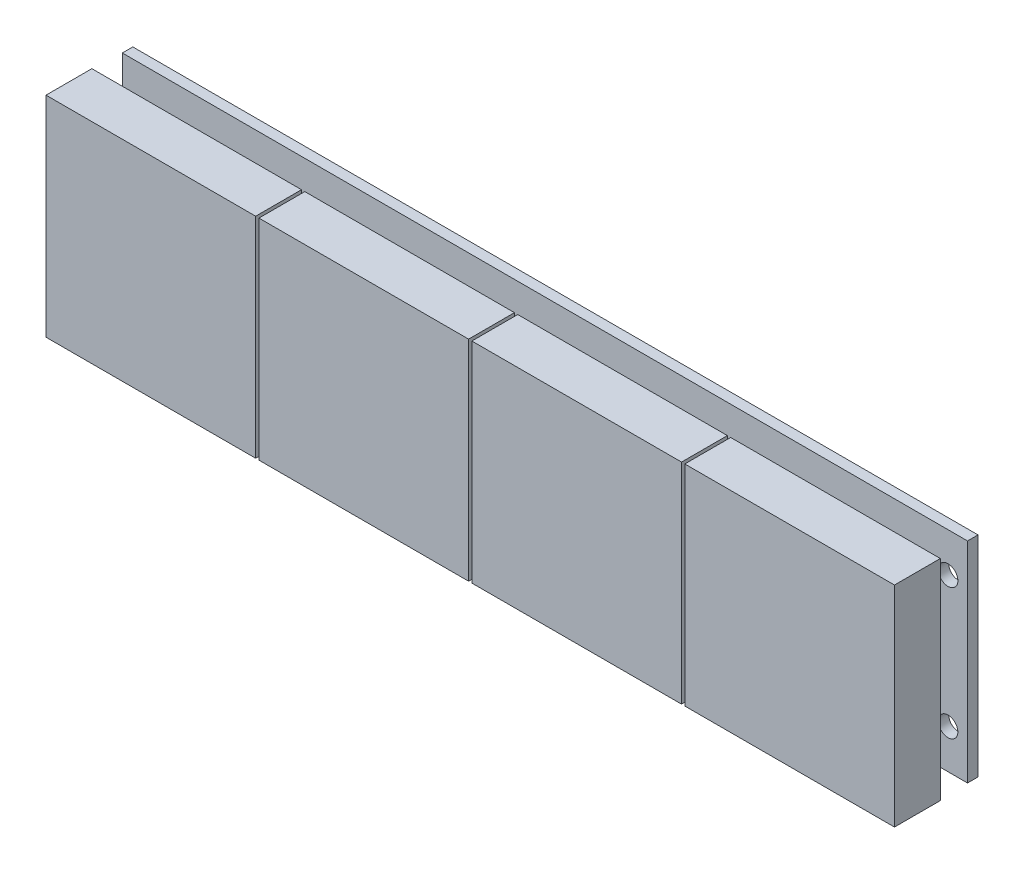
SolidWorks part; units mm, degrees
material "ABS"
ref_plane "TOP" through (0, 0, 0) normal (0, 0, 1) x (1, 0, 0)
ref_plane "FRONT" through (0, 0, 0) normal (0, 1, 0) x (1, 0, 0)
ref_plane "RIGHT" through (0, 0, 0) normal (1, 0, 0) x (0, 0, -1)
sketch "Эскиз1" plane through (0, 0, 0) normal (0, 0, 1) x (1, 0, 0)
  line L0 (-2.975, 10) -> (0, 10) construction
  line L1 (-64.5, 16) -> (64.5, 16)
  line L2 (-64.5, 16) -> (-64.5, -16)
  line L3 (-64.5, -16) -> (64.5, -16)
  line L4 (64.5, 16) -> (64.5, -16)
  line L5 (0, -16) -> (0, 16) construction
  line L6 (-64.5, 0) -> (64.5, 0) construction
  line L7 (-61.525, 10) -> (-35.225, 10) construction
  line L8 (-61.525, 10) -> (-61.525, -10) construction
  line L9 (-61.525, -10) -> (-35.225, -10) construction
  line L10 (-35.225, 10) -> (-35.225, -10) construction
  line L11 (-48.375, -10) -> (-48.375, 10) construction
  line L12 (61.525, 10) -> (64.5, 10) construction
  circle A1 centre (-61.525, 10) radius 1.5
  circle A2 centre (-61.525, -10) radius 1.5
  circle A3 centre (-35.225, -10) radius 1.5
  circle A4 centre (-35.225, 10) radius 1.5
  circle A5 centre (-29.275, 10) radius 1.5
  circle A6 centre (-29.275, -10) radius 1.5
  circle A7 centre (-2.975, 10) radius 1.5
  circle A8 centre (-2.975, -10) radius 1.5
  circle A9 centre (2.975, 10) radius 1.5
  circle A10 centre (2.975, -10) radius 1.5
  circle A11 centre (29.275, 10) radius 1.5
  circle A12 centre (29.275, -10) radius 1.5
  circle A13 centre (35.225, 10) radius 1.5
  circle A14 centre (35.225, -10) radius 1.5
  circle A15 centre (61.525, 10) radius 1.5
  circle A16 centre (61.525, -10) radius 1.5
  point P11 (-35.225, 0)
  point P36 (0, 0)
  dimension "D3" = 20
  dimension "D5" = 3
  dimension "D1" = 32
  dimension "D2" = 129
  dimension "D4" = 26.3
  dimension "D6" = 4
extrude "Бобышка-Вытянуть1" add sketch "Эскиз1" along normal blind 1.6
sketch "Эскиз2" plane through (0, 0, 1.6) normal (0, 0, 1) x (1, 0, 0)
  line L0 (-64.5, 0) -> (64.5, 0) construction
  line L1 (-64.75, 16) -> (-32.75, 16)
  line L2 (-64.75, 16) -> (-64.75, -16)
  line L3 (-64.75, -16) -> (-32.75, -16)
  line L4 (-32.75, 16) -> (-32.75, -16)
  line L5 (-64.5, 16) -> (-64.5, -16) construction
  line L6 (64.5, -16) -> (64.5, 16) construction
  line L9 (-32.25, 16) -> (-0.25, 16)
  line L10 (-0.25, 16) -> (-0.25, -16)
  line L11 (-32.25, -16) -> (-0.25, -16)
  line L12 (-32.25, 16) -> (-32.25, -16)
  line L13 (0.25, 16) -> (32.25, 16)
  line L14 (32.25, 16) -> (32.25, -16)
  line L15 (0.25, -16) -> (32.25, -16)
  line L16 (0.25, 16) -> (0.25, -16)
  line L17 (32.75, 16) -> (64.75, 16)
  line L18 (64.75, 16) -> (64.75, -16)
  line L19 (32.75, -16) -> (64.75, -16)
  line L20 (32.75, 16) -> (32.75, -16)
  line L21 (0, 16) -> (0, -16) construction
  line L22 (64.5, 16) -> (-64.5, 16) construction
  line L23 (-64.5, -16) -> (64.5, -16) construction
  point P4 (-64.75, 0)
  dimension "D1" = 4
  dimension "D2" = 32
  dimension "D3" = 0.5
  dimension "D4" = 129.5
extrude "Бобышка-Вытянуть2" add sketch "Эскиз2" along normal blind 7 from offset 4.4 separate body
